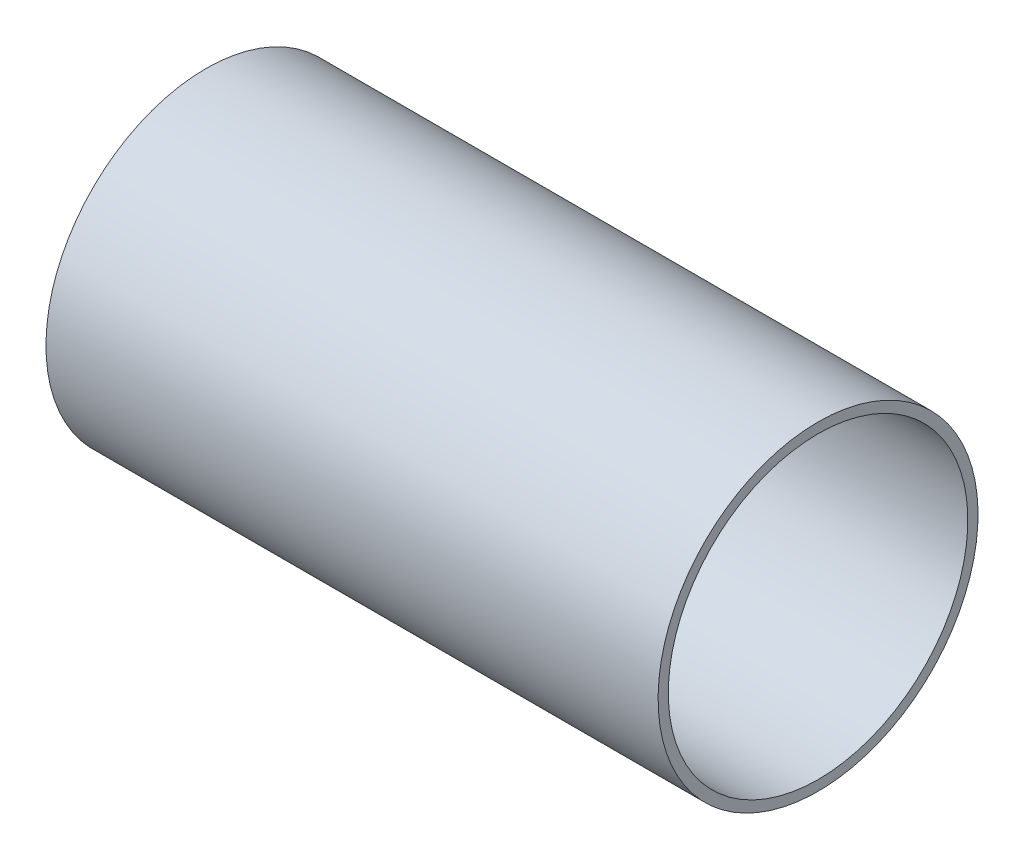
SolidWorks part; units mm, degrees
ref_plane "Front Plane" through (0, 0, 0) normal (0, 0, 1) x (1, 0, 0)
ref_plane "Top Plane" through (0, 0, 0) normal (0, 1, 0) x (1, 0, 0)
ref_plane "Right Plane" through (0, 0, 0) normal (1, 0, 0) x (0, 0, -1)
sketch "Sketch1" plane through (0, 0, 0) normal (0, 0, 1) x (1, 0, 0)
  line L0 (304.8, 49.784) -> (304.8, 0)
  line L1 (304.8, 0) -> (0, 0)
  line L2 (0, 0) -> (0, 11.7484)
  spline S0 degree 4 poles (-29.5658, 3.8633) (-28.9441, 4.0374) (-27.7007, 4.3845) (-25.2159, 5.0746) (-22.1117, 5.9273) (-19.0277, 6.7655) (-15.9353, 7.5966) (-13.5064, 8.2445) (-11.0138, 8.9031) (-8.6496, 9.5239) (-6.017, 10.2074) (-3.9348, 10.7459) (-0.8664, 11.529) (0.5497, 11.8883) (3.0854, 12.5273) (5.1062, 13.0323) (7.1101, 13.5293) (9.1599, 14.0344) (11.1954, 14.5321) (13.2334, 15.0269) (15.805, 15.6465) (18.9103, 16.3873) (22.5507, 17.2447) (26.7272, 18.2131) (31.9522, 19.4057) (42.4129, 21.7425) (62.3339, 25.9764) (110.7705, 35.2251) (160.7073, 42.1599) (207.7023, 46.435) (245.168, 48.3682) (253.7348, 48.741) (260.1614, 48.9835) (264.4463, 49.1304) (268.7317, 49.2625) (273.0175, 49.3798) (277.3037, 49.4823) (281.5902, 49.5699) (285.3296, 49.6334) (288.5217, 49.6785) (291.1667, 49.7098) (293.2638, 49.7311) (295.3592, 49.7488) (297.4702, 49.763) (299.5351, 49.7737) (301.6172, 49.7807) (304.2305, 49.7845) (305.6886, 49.7842) (308.8437, 49.7793) (310.9886, 49.769) (313.6963, 49.7536) (316.1321, 49.733) (318.7003, 49.7073) (321.2035, 49.6765) (323.7502, 49.6404) (326.2925, 49.5988) (328.8544, 49.5518) (331.4237, 49.4993) (333.3523, 49.4559) (334.6374, 49.4252) (335.2799, 49.4094) knots 0 0 0 0 0 0.006994 0.013988 0.027976 0.034844 0.041712 0.048579 0.055447 0.062315 0.069182 0.07605 0.082918 0.088602 0.094285 0.099969 0.105653 0.111336 0.11702 0.122704 0.128387 0.140005 0.151623 0.163241 0.174859 0.198094 0.267801 0.38398 0.709279 0.744133 0.778986 0.790604 0.802222 0.81384 0.825458 0.837075 0.848693 0.860311 0.871929 0.877613 0.883296 0.88898 0.894664 0.900347 0.906031 0.911715 0.917398 0.92424 0.931081 0.937923 0.944764 0.951606 0.958447 0.965289 0.97213 0.979098 0.986065 0.993033 1 1 1 1 1 construction
  spline S1 degree 4 poles (0, 11.7484) (0.4242, 11.8559) (1.2778, 12.0717) (3.0854, 12.5273) (5.1062, 13.0323) (7.1101, 13.5293) (9.1599, 14.0344) (11.1954, 14.5321) (13.2334, 15.0269) (15.805, 15.6465) (18.9103, 16.3873) (22.5507, 17.2447) (26.7272, 18.2131) (31.9522, 19.4057) (42.4129, 21.7425) (62.3339, 25.9764) (110.7705, 35.2251) (160.7073, 42.1599) (207.7023, 46.435) (245.168, 48.3682) (253.7348, 48.741) (260.1614, 48.9835) (264.4463, 49.1304) (268.7317, 49.2625) (273.0175, 49.3798) (277.3037, 49.4823) (281.5902, 49.5699) (285.3296, 49.6334) (288.5217, 49.6785) (291.1667, 49.7098) (293.2638, 49.7311) (295.3592, 49.7488) (297.4702, 49.763) (299.5351, 49.7737) (301.6172, 49.7807) (303.4822, 49.7834) (304.3624, 49.784) (304.8, 49.784) knots 0.082918 0.082918 0.082918 0.082918 0.082918 0.088602 0.094285 0.099969 0.105653 0.111336 0.11702 0.122704 0.128387 0.140005 0.151623 0.163241 0.174859 0.198094 0.267801 0.38398 0.709279 0.744133 0.778986 0.790604 0.802222 0.81384 0.825458 0.837075 0.848693 0.860311 0.871929 0.877613 0.883296 0.88898 0.894664 0.900347 0.906031 0.911715 0.917398 0.917398 0.917398 0.917398 0.917398
  dimension "D1" = 49.784
  dimension "D2" = 304.8
revolve "Revolve1" add sketch "Sketch1" angle 360 about L1
sketch "Sketch2" plane through (304.8, 0, 0) normal (1, 0, 0) x (0, 0, -1)
  circle A0 centre (0, 0) radius 49.784
extrude "Boss-Extrude1" add sketch "Sketch2" along normal blind 203.2
sketch "Sketch3" plane through (0, 0, 0) normal (-1, 0, 0) x (0, 0, 1)
  circle A0 centre (0, 0) radius 11.7484
extrude "Boss-Extrude2" add sketch "Sketch3" along normal blind 50.8
ref_plane "Plane1" through (317.5, 0, 0) normal (1, 0, 0) x (0, 0, -1)
sketch "Sketch4" plane through (317.5, 0, 0) normal (1, 0, 0) x (0, 0, -1)
  circle A0 centre (0, 0) radius 53.8852
extrude "Cut-Extrude1" cut sketch "Sketch4" against normal through all
shell "Shell1" thickness 3.175
